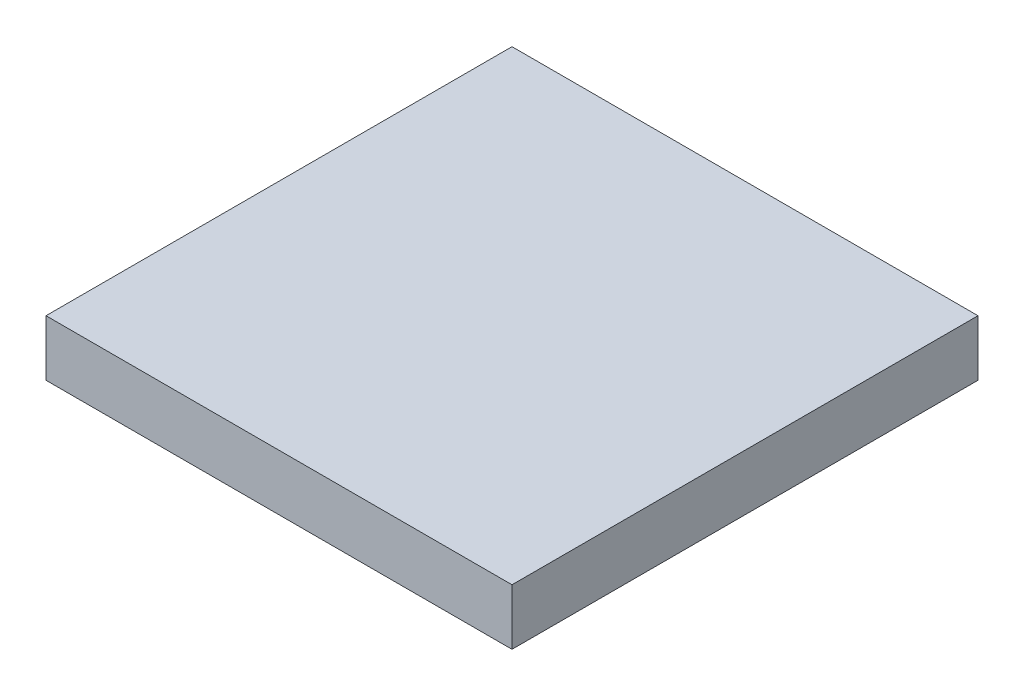
SolidWorks part; units mm, degrees
ref_plane "Front Plane" through (0, 0, 0) normal (0, 0, 1) x (1, 0, 0)
ref_plane "Top Plane" through (0, 0, 0) normal (0, 1, 0) x (1, 0, 0)
ref_plane "Right Plane" through (0, 0, 0) normal (1, 0, 0) x (0, 0, -1)
sketch "Sketch1" plane through (0, 0, 0) normal (0, 1, 0) x (1, 0, 0)
  line L1 (-12.5, -12.5) -> (12.5, -12.5)
  line L2 (-12.5, -12.5) -> (-12.5, 12.5)
  line L3 (-12.5, 12.5) -> (12.5, 12.5)
  line L4 (12.5, -12.5) -> (12.5, 12.5)
  line L5 (-12.5, -12.5) -> (12.5, 12.5) construction
  line L6 (-12.5, 12.5) -> (12.5, -12.5) construction
  point P0 (0, 0)
  dimension "D1" = 25
  dimension "D2" = 25
extrude "Boss-Extrude1" add sketch "Sketch1" along normal blind 3
sketch "Sketch2" plane through (0, 0, 0) normal (0, -1, 0) x (1, 0, 0)
  line L1 (-10, -10) -> (10, -10)
  line L2 (-10, -10) -> (-10, 10)
  line L3 (-10, 10) -> (10, 10)
  line L4 (10, -10) -> (10, 10)
  line L5 (-10, -10) -> (10, 10) construction
  line L6 (-10, 10) -> (10, -10) construction
  circle A0 centre (0, 0) radius 5
  point P0 (0, 0)
  dimension "D3" = 10
  dimension "D1" = 20
  dimension "D2" = 20
extrude "Cut-Extrude1" cut sketch "Sketch2" against normal blind 2
sketch "Sketch3" plane through (0, 0, 0) normal (0, -1, 0) x (1, 0, 0)
  line L0 (-12.5, 12.5) -> (12.5, 12.5) construction
  line L1 (-12.5, -12.5) -> (-12.5, 12.5) construction
  line L2 (12.5, 12.5) -> (12.5, -12.5) construction
  line L3 (12.5, -12.5) -> (-12.5, -12.5) construction
  circle A0 centre (-11, 11) radius 1.25
  circle A1 centre (11, 11) radius 1.25
  circle A2 centre (11, -11) radius 1.25
  circle A3 centre (-11, -11) radius 1.25
  dimension "D1" = 2.5
  dimension "D4" = 2.5
  dimension "D7" = 2.5
  dimension "D10" = 2.5
  dimension "D2" = 1.5
  dimension "D3" = 1.5
  dimension "D5" = 1.5
  dimension "D6" = 1.5
  dimension "D8" = 1.5
  dimension "D9" = 1.5
  dimension "D11" = 1.5
  dimension "D12" = 1.5
extrude "Cut-Extrude2" cut sketch "Sketch3" against normal blind 2
